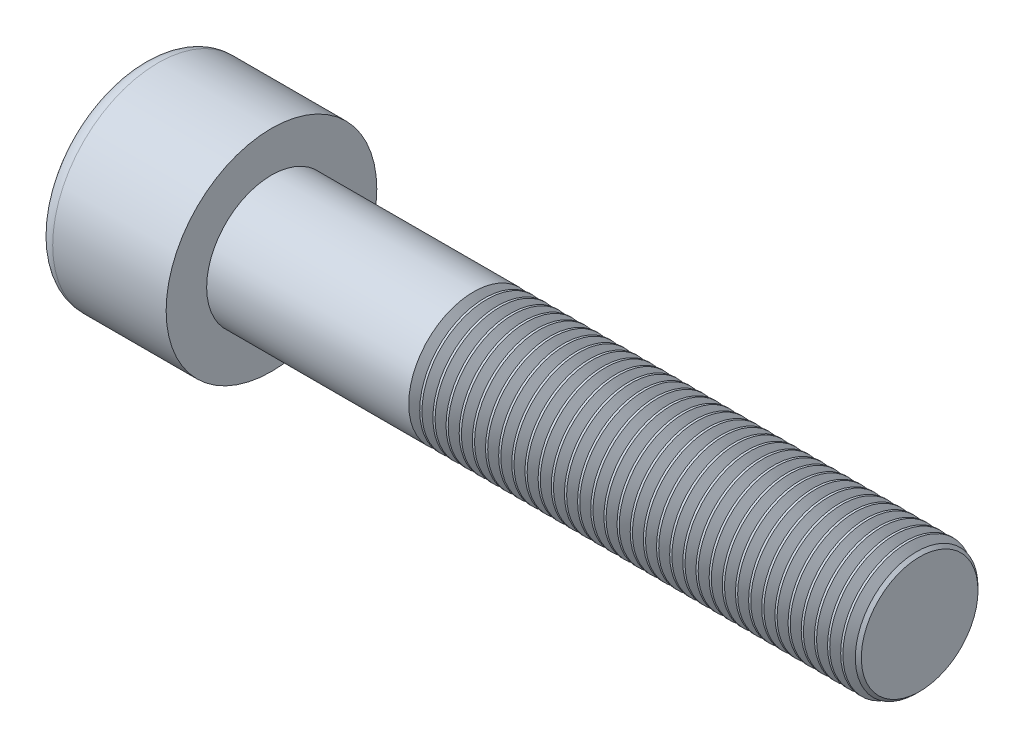
SolidWorks part; units mm, degrees
ref_plane "Front" through (0, 0, 0) normal (0, 0, 1) x (1, 0, 0)
ref_plane "Top" through (0, 0, 0) normal (0, 1, 0) x (1, 0, 0)
ref_plane "Right" through (0, 0, 0) normal (1, 0, 0) x (0, 0, -1)
sketch "Sketch1" plane through (0, 0, 0) normal (1, 0, 0) x (0, 0, -1)
  circle A0 centre (0, 0) radius 6.5
  dimension "dk" = 13
extrude "BaseHead" add sketch "Sketch1" along normal blind 8
sketch "Sketch2" plane through (8, 0, 0) normal (1, 0, 0) x (0, 0, -1)
  circle A0 centre (0, 0) radius 4
  dimension "d" = 8
extrude "BaseBody" add sketch "Sketch2" along normal blind 40
cosmetic thread "ThreadCosmetic1" [suppressed] parameters "b"=28, "D2"=6.647
sketch "Sketch3" plane through (0, 0, 0) normal (1, 0, 0) x (0, 0, -1)
  line L1 (3.4641, 0) -> (1.7321, 3)
  line L2 (1.7321, 3) -> (-1.7321, 3)
  line L3 (-1.7321, 3) -> (-3.4641, 0)
  line L4 (-3.4641, 0) -> (-1.7321, -3)
  line L5 (-1.7321, -3) -> (1.7321, -3)
  line L6 (1.7321, -3) -> (3.4641, 0)
  circle A0 centre (0, 0) radius 3 construction
  dimension "s" = 6
  dimension "e" = 6.9282
extrude "HexagonSocket" cut sketch "Sketch3" along normal blind 4
sketch "Sketch4" plane through (-4.1961, 0.75, 0) normal (0, 0, 1) x (-1, 0, 0)
  line L0 (-8.1961, 3.75) -> (-9.9282, 0.75)
  line L2 (-9.9282, 0.75) -> (-8.1961, 0.75)
  line L3 (-8.1961, 0.75) -> (-8.1961, 3.75)
  line L4 (-5.0351, 0.75) -> (0.839, 0.75) construction
  line L5 (-52.1961, 0.75) -> (-12.1961, 0.75) construction
  line L6 (-12.1961, 0.75) -> (-4.1961, 0.75) construction
  dimension "m" = 60
revolve "Cut-Revolve1" cut sketch "Sketch4" angle 360 about L4
fillet "HeadFillet" [suppressed] radius 0.4
fillet "TopFillet" radius 1 1 edges at (0, 0, -6.5)
chamfer "Chamfer1" distance 0.4 angle 45 1 edges at (48, 0, -4)
sketch "Sketch5" plane through (0, 0, 0) normal (0, 0, 1) x (1, 0, 0)
  line L0 (47.6, 3.4141) -> (47.9382, 4)
  line L1 (47.9382, 4) -> (47.9382, 4.6765)
  line L2 (47.9382, 4.6765) -> (47.2617, 4.6765)
  line L3 (47.2617, 4.6765) -> (47.2617, 4)
  line L4 (47.2617, 4) -> (47.6, 3.4141)
  line L5 (0, 0) -> (7.8886, 0) construction
  line L6 (47.6, -4) -> (47.6, 4) construction
  dimension "D1" = 8
  dimension "D2" = 0.6765
revolve "Cut-Revolve10" cut sketch "Sketch5" angle 360 about L5
pattern_linear "LPattern10" count 34 spacing 0.8118 along (-1, 0, 0) of "Cut-Revolve10"
equation "\"r1@TopFillet\" = \"d@Sketch2\" / 8"
equation "\"D1@Chamfer1\" = \"r@HeadFillet\""
equation "\"D1@Sketch5\" = \"d@Sketch2\""
equation "\"D2@Sketch5\" =  ( \"d@Sketch2\" - \"D2@ThreadCosmetic1\" )  / 2"
equation "\"D3@LPattern10\" = \"D2@Sketch5\" * 1.2"
equation "\"D1@LPattern10\" = \"b@ThreadCosmetic1\" / \"D3@LPattern10\""
